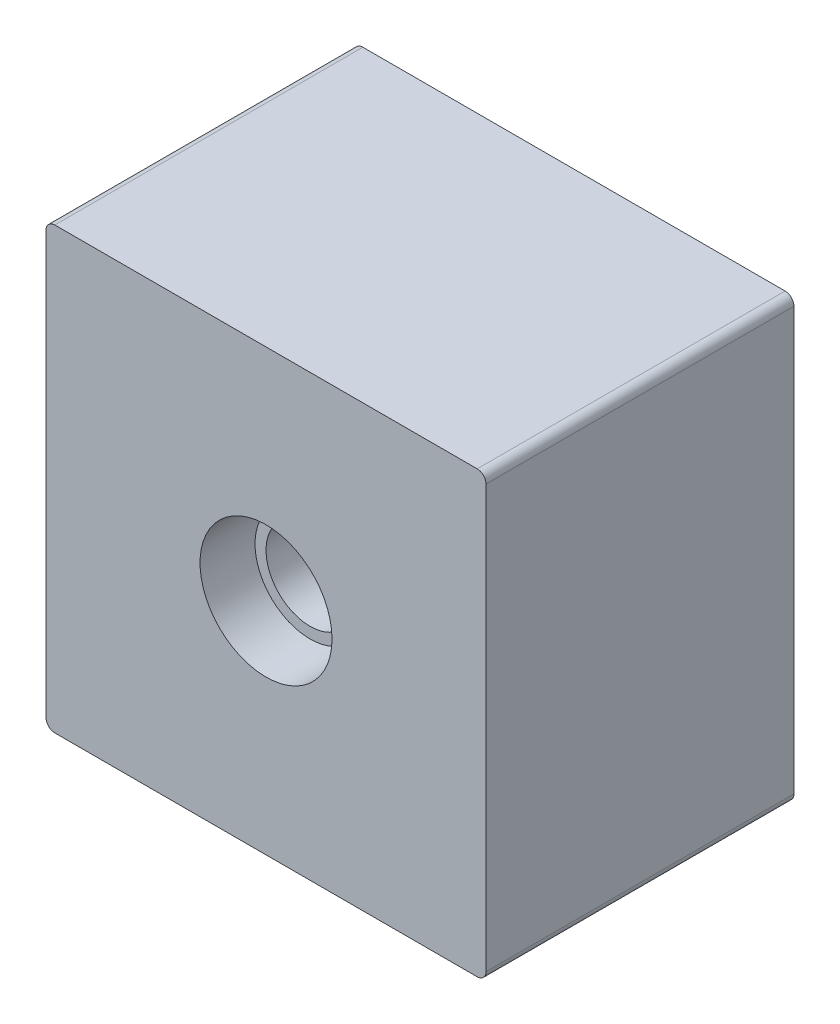
SolidWorks part; units mm, degrees
material "201 Annealed Stainless Steel (SS)"
ref_plane "Front Plane" through (0, 0, 0) normal (0, 0, 1) x (1, 0, 0)
ref_plane "Top Plane" through (0, 0, 0) normal (0, 1, 0) x (1, 0, 0)
ref_plane "Right Plane" through (0, 0, 0) normal (1, 0, 0) x (0, 0, -1)
sketch "Sketch1" plane through (0, 0, 0) normal (0, 0, 1) x (1, 0, 0)
  line L1 (5, 5) -> (-5, 5)
  line L2 (5, 5) -> (5, -5)
  line L3 (5, -5) -> (-5, -5)
  line L4 (-5, 5) -> (-5, -5)
  line L5 (5, 5) -> (-5, -5) construction
  line L6 (5, -5) -> (-5, 5) construction
  point P0 (0, 0)
  dimension "D1" = 10
  dimension "D2" = 10
extrude "Boss-Extrude1" add sketch "Sketch1" along normal blind 7
sketch "Sketch2" plane through (0, 0, 7) normal (0, 0, 1) x (1, 0, 0)
  circle A0 centre (0, 0) radius 1.5
  dimension "D1" = 3
extrude "Cut-Extrude1" cut sketch "Sketch2" against normal blind 3
sketch "Sketch3" plane through (0, 0, 4) normal (0, 0, 1) x (1, 0, 0)
  circle A0 centre (0, 0) radius 1
  circle A1 centre (0, 0) radius 1.25
  dimension "D1" = 2
  dimension "D2" = 2.5
extrude "Boss-Extrude2" add sketch "Sketch3" along normal blind 2
sketch "Sketch4" plane through (0, 0, 4) normal (0, 0, 1) x (1, 0, 0)
  circle A0 centre (0, 0) radius 0.5
  dimension "D1" = 1
ref_plane "Plane2" through (0, 0, 5) normal (0, 0, 1) x (1, 0, 0)
sketch "Sketch5" plane through (0, 0, 5) normal (0, 0, 1) x (1, 0, 0)
  circle A0 centre (0, 0) radius 0.5 construction
  circle A1 centre (0, 0) radius 0.5
sketch "Sketch7" plane through (0, 0, 5) normal (0, 0, 1) x (1, 0, 0)
  line L0 (-0.0869, 0.4924) -> (-0.1738, 0.9848)
  line L1 (0.0869, 0.4924) -> (0.1738, 0.9848)
  circle A0 centre (0, 0) radius 1 construction
  arc A1 (0.1738, 0.9848) -> (-0.1738, 0.9848) centre (0, 0) ccw
  circle A2 centre (0, 0) radius 0.5 construction
  arc A3 (0.0869, 0.4924) -> (-0.0869, 0.4924) centre (0, 0) ccw
surface "Surface-Plane3" sketch "Sketch7"
pattern_circular "CirPattern1" count 15 over 360 about axis through (0, 0, 6) along (0, 0, -1) of bodies 104
fillet "Fillet1" radius 0.2 4 edges at (-5, 5, 3.5) (-5, -5, 3.5) (5, -5, 3.5) (5, 5, 3.5)
